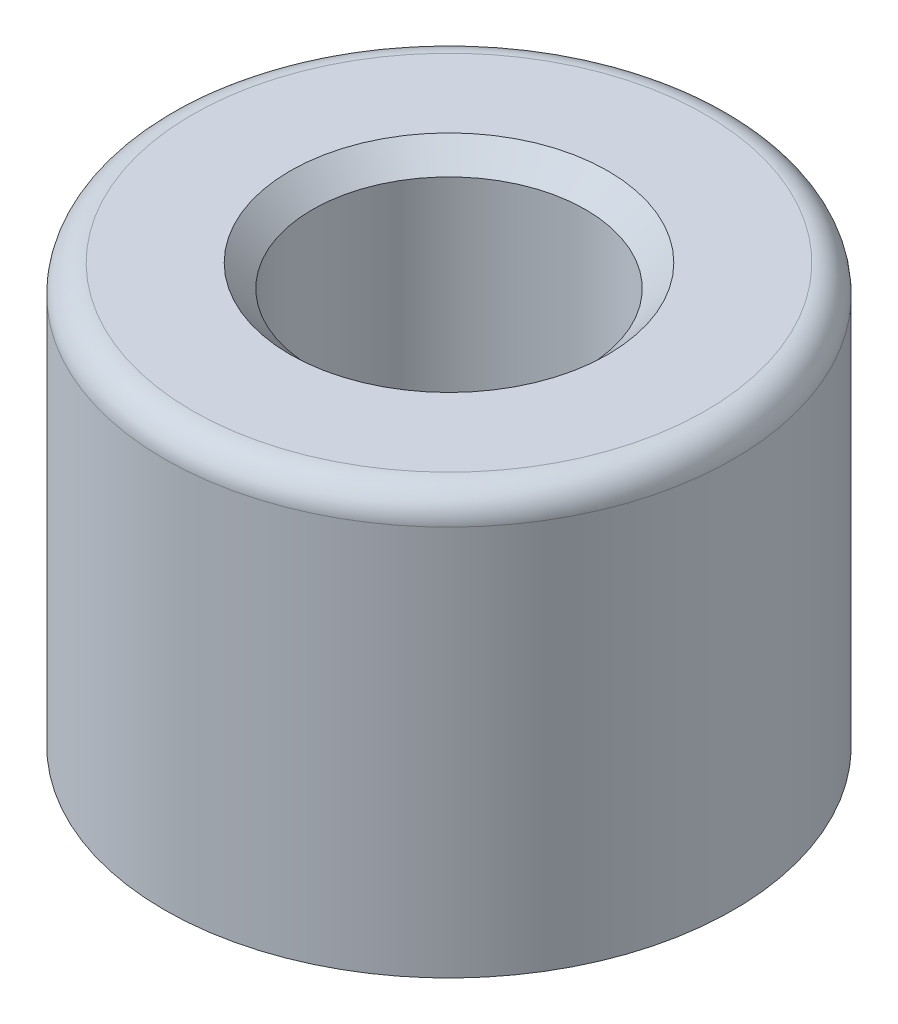
SolidWorks part; units mm, degrees
ref_plane "Front Plane" through (0, 0, 0) normal (0, 0, 1) x (1, 0, 0)
ref_plane "Top Plane" through (0, 0, 0) normal (0, 1, 0) x (1, 0, 0)
ref_plane "Right Plane" through (0, 0, 0) normal (1, 0, 0) x (0, 0, -1)
sketch "Sketch1" plane through (0, 0, 0) normal (0, 1, 0) x (1, 0, 0)
  circle A0 centre (0, 0) radius 6.477
  dimension "D1" = 12.954
extrude "Boss-Extrude1" add sketch "Sketch1" along normal blind 9.525
fillet "Fillet1" radius 0.635 1 edges at (0, 9.525, 6.477)
hole_wizard "1/4-20 Tapped Hole1" positions "Sketch5" profile "Sketch6" tap size "1/4-20" standard "ANSI Inch"
sketch "Sketch5" plane through (0, 9.525, 0) normal (0, 1, 0) x (1, 0, 0)
  point P0 (0, 0)
sketch "Sketch6" plane through (0, 9.525, 0) normal (1, 0, 0) x (0, 0, 1)
  line L0 (0, 0) -> (0, 11.3946)
  line L1 (0, 11.3946) -> (3.1115, 9.525)
  line L2 (3.1115, 9.525) -> (3.1115, 0)
  line L5 (3.1115, 0) -> (0, 0)
  line L10 (0, 11.3946) -> (-3.1115, 9.525) construction
  line L11 (0, -6.35) -> (0, 107.95) construction
  dimension "Tap Drill Dia." = 6.223
  dimension "Tap Drill Depth" = 9.525
  dimension "Drill Angle" = 118
cosmetic thread "Hole Thread1" parameters "D1"=12.7, "D2"=6.35
chamfer "Chamfer1" distance 0.508 angle 45 1 edges at (0, 9.525, 3.1115)
